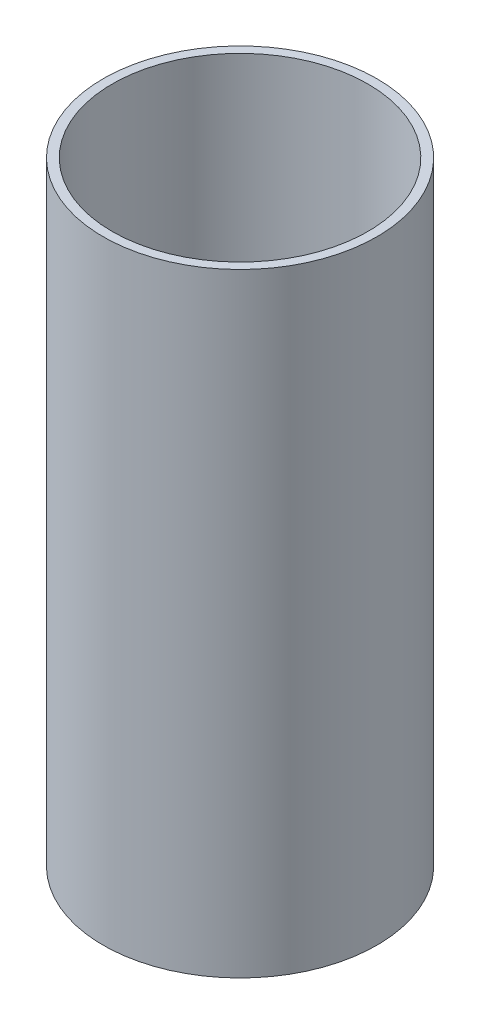
SolidWorks part; units mm, degrees
ref_plane "Front Plane" through (0, 0, 0) normal (0, 0, 1) x (1, 0, 0)
ref_plane "Top Plane" through (0, 0, 0) normal (0, 1, 0) x (1, 0, 0)
ref_plane "Right Plane" through (0, 0, 0) normal (1, 0, 0) x (0, 0, -1)
sketch "Sketch1" plane through (0, 0, 0) normal (0, 0, 1) x (1, 0, 0)
  line L8 (25.4508, 0) -> (27.2542, 0)
  line L9 (25.4508, 0) -> (25.4508, 122.1486)
  line L10 (25.4508, 122.1486) -> (27.2542, 122.1486)
  line L11 (27.2542, 0) -> (27.2542, 122.1486)
  dimension "D1" = 122.1486
  dimension "D2" = 1.8034
  dimension "D3" = 27.2542
ref_axis "Central Axis" through (0, -8.89, 0) along (0, 1, 0)
revolve "Revolve1" add sketch "Sketch1" angle 360 about axis through (0, -8.89, 0) along (0, 1, 0)
